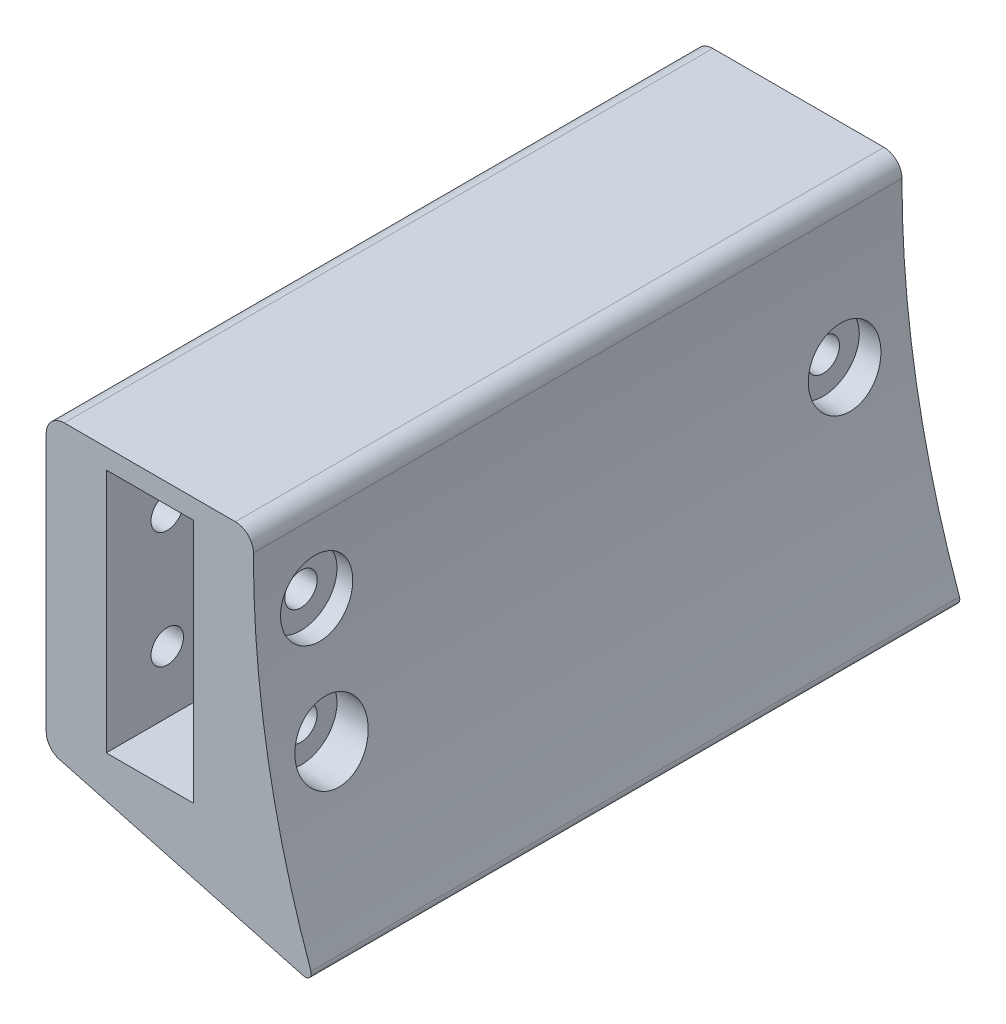
SolidWorks part; units mm, degrees
ref_plane "Plan de face" through (0, 0, 0) normal (0, 0, 1) x (1, 0, 0)
ref_plane "Plan de dessus" through (0, 0, 0) normal (0, 1, 0) x (1, 0, 0)
ref_plane "Plan de droite" through (0, 0, 0) normal (1, 0, 0) x (0, 0, -1)
sketch "Esquisse1" plane through (0, 0, 0) normal (0, 0, 1) x (1, 0, 0)
  line L0 (-7.27, 0) -> (7.27, 0)
  line L1 (-7.27, 0) -> (-7.27, 40.8)
  line L3 (-17.27, 44.0848) -> (-17.27, -4.2604)
  line L5 (0, -33.0252) -> (0, 33.0252) construction
  line L8 (7.27, 0) -> (7.27, 40.8)
  line L9 (-17.27, -4.2604) -> (27.46, -16.2458)
  line L14 (-7.27, 40.8) -> (7.27, 40.8)
  line L15 (-17.27, 44.0848) -> (17.27, 44.0848)
  arc A0 (17.27, 44.0848) -> (27.46, -16.2458) centre (180.9557, 40.7059) ccw
  point P4 (0, 0)
  point P12 (0, -2.3461)
  dimension "D1" = 14.54
  dimension "D2" = 15
  dimension "D3" = 40.8
  dimension "D4" = 10
extrude "Boss.-Extru.1" add sketch "Esquisse1" along normal blind 108
hole_wizard "Dégagement M1.62" positions "Esquisse4" profile "Esquisse5" hole size "M1.6" standard "Ansi Metric" end condition through all
sketch "Esquisse4" plane through (-17.27, 0, 0) normal (-1, 0, 0) x (0, 0, 1)
  point P0 (10.8725, 20)
  point P4 (97.8442, 29.7004)
  point P7 (97.8442, 10.2996)
sketch "Esquisse5" plane through (-17.27, 20, 10.8725) normal (0, 1, 0) x (0, 0, 1)
  line L0 (0, 0) -> (0, 44.73)
  line L1 (0, 44.73) -> (2.7, 44.73)
  line L2 (2.7, 44.73) -> (2.7, 0)
  line L5 (2.7, 0) -> (0, 0)
  line L11 (0, -6.35) -> (0, 107.95) construction
  dimension "Diamètre du perçage jusqu'au prochain" = 5.4
  dimension "Profondeur du perçage jusqu'au prochain" = 44.73
fillet "Congé1" radius 3 3 edges at (17.27, 44.0848, 54) (-17.27, 44.0848, 54) (-17.27, -4.2604, 54)
fillet "Congé2" radius 1 1 edges at (27.46, -16.2458, 54)
ref_plane "Plan1" through (30, 0, 0) normal (1, 0, 0) x (0, 0, -1)
sketch "Esquisse6" plane through (30, 0, 0) normal (1, 0, 0) x (0, 0, -1)
  circle A0 centre (-10.8725, 20) radius 6
  circle A1 centre (-97.8442, 29.7004) radius 6
  circle A2 centre (-97.8442, 10.2996) radius 6
  dimension "D1" = 12
extrude "Enlèv. mat.-Extru.1" cut sketch "Esquisse6" against normal blind 15
sketch "Esquisse7" plane through (-17.27, 0, 0) normal (-1, 0, 0) x (0, 0, 1)
  line L1 (13.7592, 15) -> (16.646, 20)
  line L2 (16.646, 20) -> (13.7592, 25)
  line L3 (13.7592, 25) -> (7.9857, 25)
  line L4 (7.9857, 25) -> (5.099, 20)
  line L5 (5.099, 20) -> (7.9857, 15)
  line L6 (7.9857, 15) -> (13.7592, 15)
  line L7 (100.731, 24.7004) -> (103.6177, 29.7004)
  line L8 (103.6177, 29.7004) -> (100.731, 34.7004)
  line L9 (100.731, 34.7004) -> (94.9575, 34.7004)
  line L10 (94.9575, 34.7004) -> (92.0707, 29.7004)
  line L11 (92.0707, 29.7004) -> (94.9575, 24.7004)
  line L12 (94.9575, 24.7004) -> (100.731, 24.7004)
  line L13 (100.731, 5.2996) -> (103.6177, 10.2996)
  line L14 (103.6177, 10.2996) -> (100.731, 15.2996)
  line L15 (100.731, 15.2996) -> (94.9575, 15.2996)
  line L16 (94.9575, 15.2996) -> (92.0707, 10.2996)
  line L17 (92.0707, 10.2996) -> (94.9575, 5.2996)
  line L18 (94.9575, 5.2996) -> (100.731, 5.2996)
  circle A0 centre (10.8725, 20) radius 5 construction
  circle A1 centre (97.8442, 29.7004) radius 5 construction
  circle A2 centre (97.8442, 10.2996) radius 5 construction
  point P11 (92.0932, 29.7004)
  point P28 (92.0707, 10.2996)
  dimension "D1" = 10
  dimension "D2" = 10
  dimension "D3" = 10
extrude "Enlèv. mat.-Extru.2" cut sketch "Esquisse7" against normal blind 3
